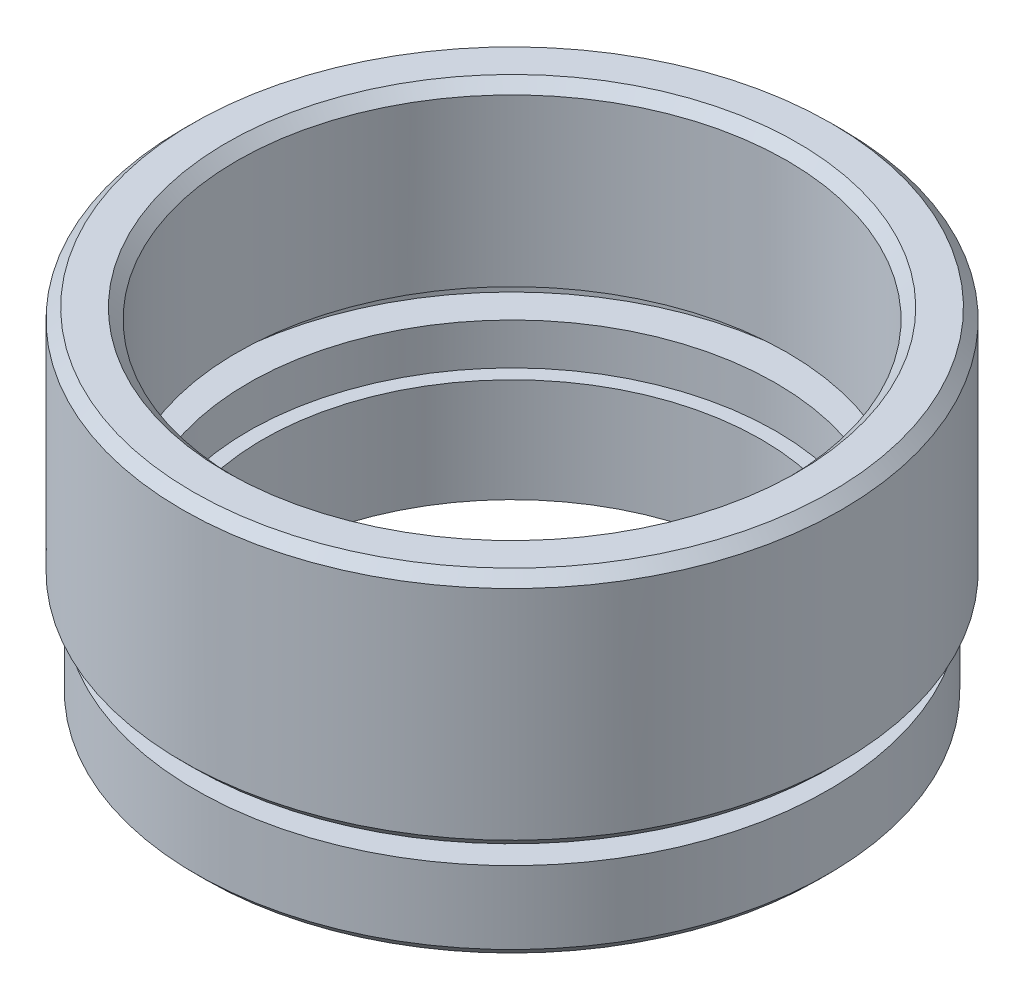
SolidWorks part; units mm, degrees
ref_plane "前视基准面" through (0, 0, 0) normal (0, 0, 1) x (1, 0, 0)
ref_plane "上视基准面" through (0, 0, 0) normal (0, 1, 0) x (1, 0, 0)
ref_plane "右视基准面" through (0, 0, 0) normal (1, 0, 0) x (0, 0, -1)
sketch "草图1" plane through (0, 0, 0) normal (0, 0, 1) x (1, 0, 0)
  line L0 (0, 0) -> (0, 21.8535) construction
  line L1 (12, 0) -> (15.25, 0)
  line L2 (15.25, 0) -> (15.25, 4)
  line L3 (15.25, 4) -> (13.75, 4)
  line L4 (13.75, 4) -> (13.75, 5)
  line L5 (13.75, 5) -> (15.875, 5)
  line L6 (15.875, 5) -> (15.875, 16.5)
  line L7 (15.875, 16.5) -> (13.25, 16.5)
  line L8 (13.25, 16.5) -> (13.25, 8)
  line L9 (13.25, 8) -> (14.35, 8)
  line L10 (14.35, 8) -> (14.35, 7)
  line L11 (14.35, 7) -> (12.7, 7)
  line L12 (12.7, 7) -> (12.7, 5)
  line L13 (12.7, 5) -> (12, 5)
  line L14 (12, 0) -> (12, 5)
  dimension "D1" = 16.5
  dimension "D2" = 15.875
  dimension "D3" = 13.25
  dimension "D4" = 12.7
  dimension "D5" = 1
  dimension "D6" = 2
  dimension "D7" = 12
  dimension "D8" = 15.25
  dimension "D9" = 1
  dimension "D10" = 5
  dimension "D11" = 5
  dimension "D12" = 14.35
  dimension "D13" = 13.75
revolve "旋转1" add sketch "草图1" angle 360 about L0
cosmetic thread "装饰螺纹线11"
cosmetic thread "装饰螺纹线12"
chamfer "倒角1" distance 0.5 angle 45 4 edges at (0, 16.5, -13.25) (0, 16.5, -15.875) (0, 5, -15.875) (0, 0, -15.25)
